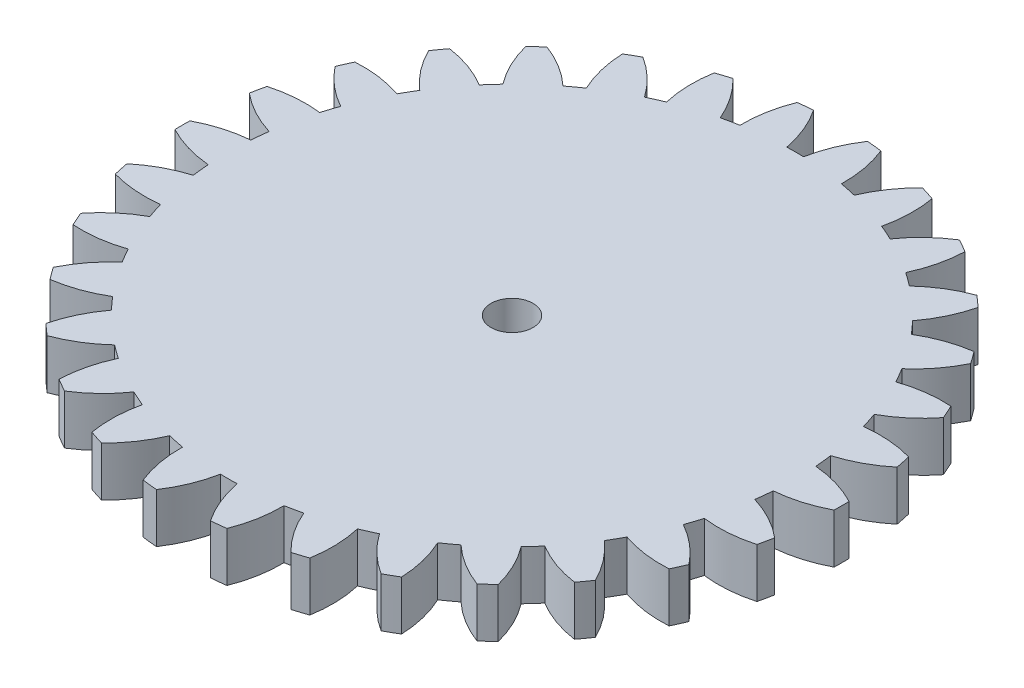
SolidWorks part; units mm, degrees
ref_plane "Front Plane" through (0, 0, 0) normal (0, 0, 1) x (1, 0, 0)
ref_plane "Top Plane" through (0, 0, 0) normal (0, 1, 0) x (1, 0, 0)
ref_plane "Right Plane" through (0, 0, 0) normal (1, 0, 0) x (0, 0, -1)
sketch "Sketch1" plane through (0, 0, 0) normal (0, 1, 0) x (1, 0, 0)
  circle A0 centre (0, 0) radius 20
  dimension "addendumDiamteter" = 40
extrude "Boss-Extrude1" add sketch "Sketch1" along normal blind 3
sketch "Sketch2" plane through (0, 3, 0) normal (0, 1, 0) x (1, 0, 0)
  line L0 (0, 0) -> (0, 28.8712) construction
  line L1 (0, 0) -> (-1.8095, 17.2166) construction
  line L3 (-0.9809, 18.7243) -> (-1.9572, 18.6217) construction
  circle A0 centre (0, 0) radius 18.75 construction
  circle A2 centre (0, 0) radius 17.1875 construction
  circle A3 centre (0, 0) radius 17.6192 construction
  arc A4 (-0.5066, 17.18) -> (0.5066, 17.18) centre (0, 0) cw
  arc A5 (-1.6375, 19.9329) -> (1.6375, 19.9329) centre (0, 0) cw
  circle A6 centre (0, 0) radius 20 construction
  arc A7 (-1.6375, 19.9329) -> (-0.5066, 17.18) centre (-7.8715, 15.7631) cw
  arc A8 (1.6375, 19.9329) -> (0.5066, 17.18) centre (7.8715, 15.7631) ccw
  dimension "dedendumCircle" = 34.375
  dimension "baseDiameter" = 35.2385
  dimension "PitchDiameter" = 37.5
  dimension "D1" = 7.5
  dimension "D4" = 6
  dimension "D2" = 0.9817
extrude "Cut-Extrude1" cut sketch "Sketch2" against normal through all
pattern_circular "CirPattern1" count 30 over 360 about axis through (0, 0, 0) along (0, 1, 0) of "Cut-Extrude1"
sketch "Sketch3" plane through (0, 3, 0) normal (0, 1, 0) x (1, 0, 0)
  line L0 (0, 2) -> (-4.1557, 9.9831)
  line L2 (4.1557, 9.9831) -> (0, 2)
  line L3 (0, 0) -> (0, 31.2074) construction
  line L4 (0, 0) -> (46.4667, 0) construction
  line L5 (-4.1557, 9.9831) -> (4.1557, 9.9831) construction
  arc A0 (-4.1557, 9.9831) -> (4.1557, 9.9831) centre (0, -1.2743) cw
  dimension "D4" = 12
  dimension "D1" = 55
  dimension "D2" = 2
  dimension "D3" = 9
extrude "Cut-Extrude2" [suppressed] cut sketch "Sketch3" against normal blind 10
fillet "Fillet1" [suppressed] radius 1
fillet "Fillet2" [suppressed] radius 1
fillet "Fillet3" [suppressed] radius 1
pattern_circular "CirPattern2" [suppressed] count 6 over 360
sketch "Sketch6" plane through (0, 3, 0) normal (0, 1, 0) x (1, 0, 0)
  line L0 (0, 0) -> (22.423, 0) construction
  line L1 (22.423, 0) -> (0, 0) construction
  line L2 (0, 0) -> (0, 27.3259) construction
  line L3 (1.3229, 1.5) -> (-1.3229, 1.5)
  arc A0 (-1.3229, 1.5) -> (1.3229, 1.5) centre (0, 0) ccw
  dimension "D1" = 2
  dimension "D2" = 1.5
extrude "Cut-Extrude5" [suppressed] cut sketch "Sketch6" against normal through all
sketch "Sketch7" plane through (0, 3, 0) normal (0, 1, 0) x (1, 0, 0)
  circle A0 centre (0, 0) radius 1.275
  dimension "D1" = 2.55
extrude "Cut-Extrude6" cut sketch "Sketch7" against normal through all
equation "\"module\"= 1.25"
equation "\"teeth\"= 30"
equation "\"pressureAngle\"= 20deg"
equation "\"gearThickness\"= 3"
equation "\"addendumFactor\"= 1"
equation "\"dedendumFactor\"= 1.25"
equation "\"pitch\"= 1 / \"module\""
equation "\"pitchDiameter\"= \"teeth\" / \"pitch\""
equation "\"addendum\"= \"addendumFactor\" / \"pitch\""
equation "\"dedendum\"= \"dedendumFactor\" / \"pitch\""
equation "\"addendumDiamteter@Sketch1\"=\"pitchDiameter\"+(\"addendum\"*2)"
equation "\"dedendumCircle@Sketch2\"=\"pitchDiameter\" -2 *\"dedendum\""
equation "\"baseDiameter@Sketch2\"=\"pitchDiameter\"*cos( \"pressureAngle\")"
equation "\"PitchDiameter@Sketch2\"=\"pitchDiameter\""
equation "\"D4@Sketch2\"=180/\"teeth\""
equation "\"D1@Sketch2\"=\"pitchDiameter\"/5"
equation "\"D2@Sketch2\"=PI / 2 / \"pitch\" / 2"
equation "\"D1@CirPattern1\"=\"teeth\""
